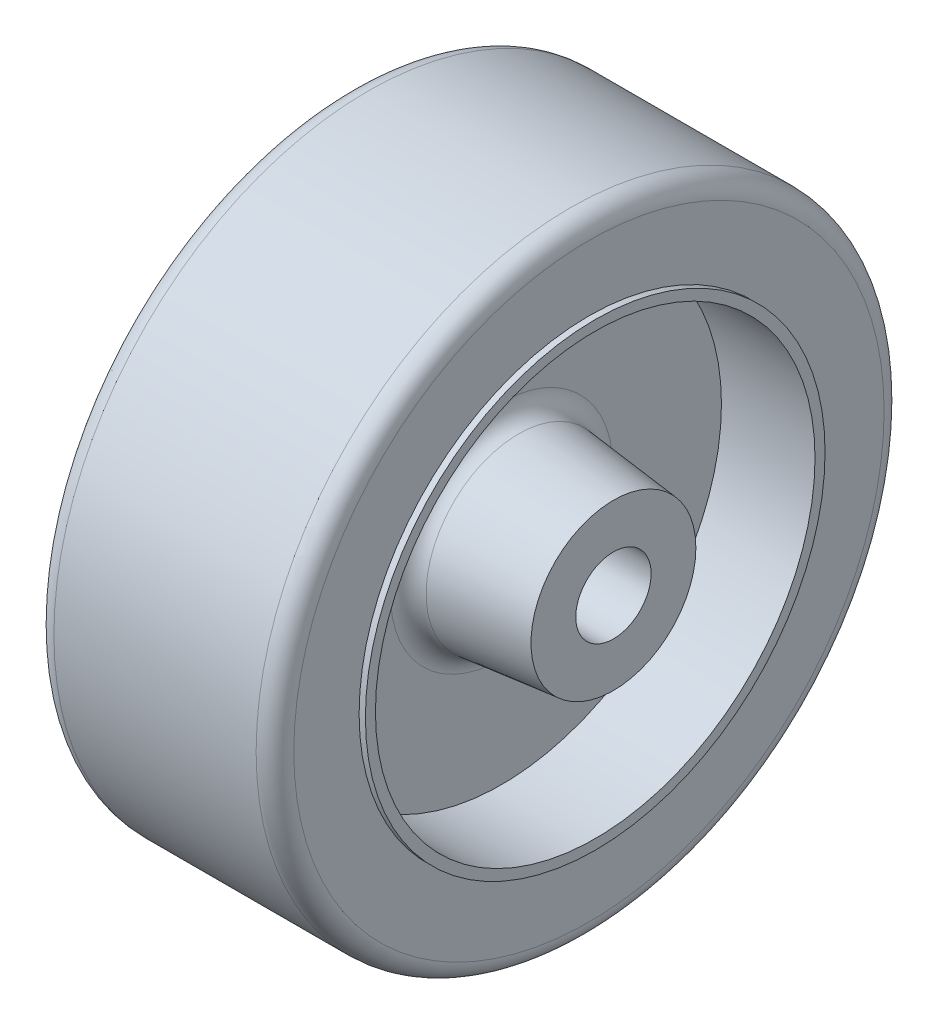
SolidWorks part; units mm, degrees
material "Plastique personnalisé"
ref_plane "Plan de face" through (0, 0, 0) normal (0, 0, 1) x (1, 0, 0)
ref_plane "Plan de dessus" through (0, 0, 0) normal (0, 1, 0) x (1, 0, 0)
ref_plane "Plan de droite" through (0, 0, 0) normal (1, 0, 0) x (0, 0, -1)
sketch "Esquisse1" plane through (0, 0, 0) normal (1, 0, 0) x (0, 0, -1)
  circle A0 centre (0, 0) radius 25
extrude "Boss.-Extru.1" add sketch "Esquisse1" along normal blind 19.1
sketch "Esquisse2" plane through (19.1, 0, 0) normal (1, 0, 0) x (0, 0, -1)
  circle A0 centre (0, 0) radius 18.3
extrude "Boss.-Extru.2" add sketch "Esquisse2" along normal blind 0.5
fillet "Congé1" radius 1.5 2 edges at (0, 0, -25) (19.1, 0, -25)
sketch "Esquisse3" plane through (0, 0, 0) normal (-1, 0, 0) x (0, 0, 1)
  circle A0 centre (0, 0) radius 18.3
extrude "Boss.-Extru.3" add sketch "Esquisse3" along normal blind 0.5
sketch "Esquisse4" plane through (-0.5, 0, 0) normal (-1, 0, 0) x (0, 0, 1)
  circle A0 centre (0, 0) radius 17.5
  dimension "D1" = 35
extrude "Enlèv. mat.-Extru.1" cut sketch "Esquisse4" against normal blind 7.45
sketch "Esquisse5" plane through (19.6, 0, 0) normal (1, 0, 0) x (0, 0, -1)
  circle A0 centre (0, 0) radius 17.5
extrude "Enlèv. mat.-Extru.2" cut sketch "Esquisse5" against normal blind 7.45
sketch "Esquisse6" plane through (12.15, 0, 0) normal (1, 0, 0) x (0, 0, -1)
  circle A0 centre (0, 0) radius 7.5
extrude "Boss.-Extru.4" add sketch "Esquisse6" along normal blind 8.9 draft 6
fillet "Congé2" radius 1.5 1 edges at (12.15, 0, -7.5)
sketch "Esquisse7" plane through (6.95, 0, 0) normal (-1, 0, 0) x (0, 0, 1)
  circle A0 centre (0, 0) radius 7.5
extrude "Boss.-Extru.5" add sketch "Esquisse7" along normal blind 8.9 draft 6
fillet "Congé3" radius 1.5 1 edges at (6.95, 0, 7.5)
sketch "Esquisse8" plane through (-1.95, 0, 0) normal (-1, 0, 0) x (0, 0, 1)
  circle A0 centre (0, 0) radius 3
extrude "Enlèv. mat.-Extru.3" cut sketch "Esquisse8" against normal blind 28.9
